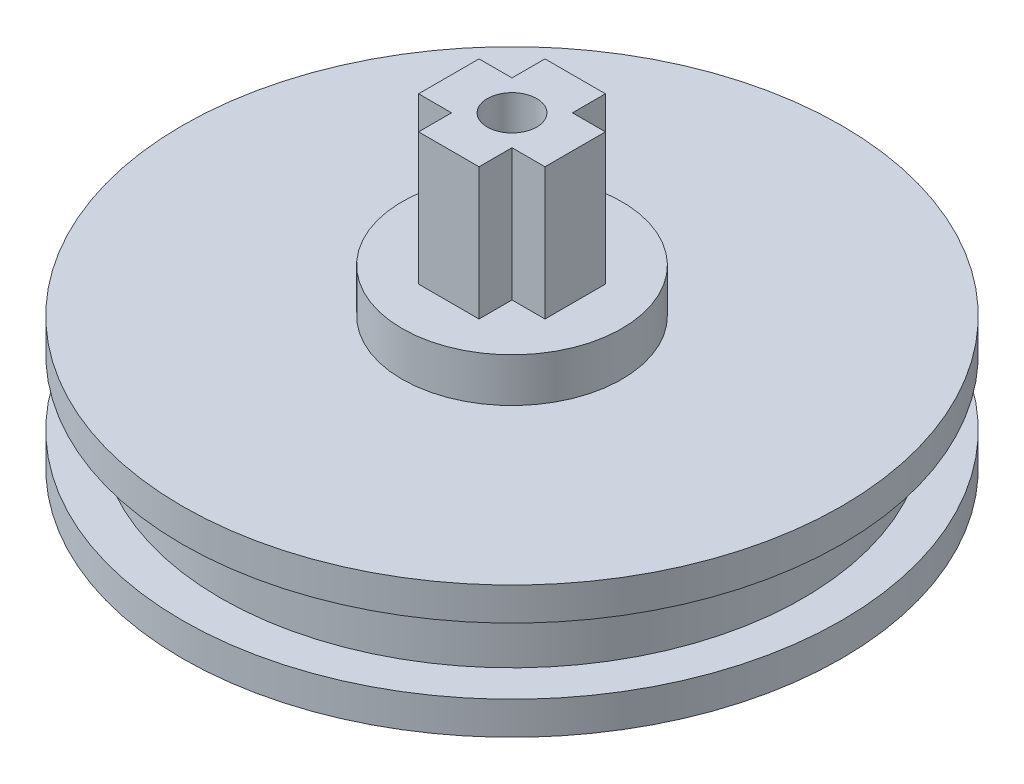
SolidWorks part; units mm, degrees
ref_plane "Front Plane" through (0, 0, 0) normal (0, 0, 1) x (1, 0, 0)
ref_plane "Top Plane" through (0, 0, 0) normal (0, 1, 0) x (1, 0, 0)
ref_plane "Right Plane" through (0, 0, 0) normal (1, 0, 0) x (0, 0, -1)
sketch "Sketch1" plane through (0, 0, 0) normal (0, 1, 0) x (1, 0, 0)
  circle A0 centre (0, 0) radius 30
extrude "c" add sketch "Sketch1" along normal blind 3
sketch "Sketch2" plane through (0, 3, 0) normal (0, 1, 0) x (1, 0, 0)
  circle A0 centre (0, 0) radius 26.5
extrude "Boss-Extrude2" add sketch "Sketch2" along normal blind 6
sketch "Sketch3" plane through (0, 9, 0) normal (0, 1, 0) x (1, 0, 0)
  circle A0 centre (0, 0) radius 30
extrude "Boss-Extrude3" add sketch "Sketch3" along normal blind 3
sketch "Sketch4" plane through (0, 12, 0) normal (0, 1, 0) x (1, 0, 0)
  line L1 (5.75, -2.75) -> (-5.75, -2.75)
  line L2 (5.75, -2.75) -> (5.75, 2.75)
  line L3 (5.75, 2.75) -> (-5.75, 2.75)
  line L4 (-5.75, -2.75) -> (-5.75, 2.75)
  line L5 (5.75, -2.75) -> (-5.75, 2.75) construction
  line L6 (5.75, 2.75) -> (-5.75, -2.75) construction
  line L7 (2.75, -5.75) -> (-2.75, -5.75)
  line L8 (2.75, -5.75) -> (2.75, 5.75)
  line L9 (2.75, 5.75) -> (-2.75, 5.75)
  line L10 (-2.75, -5.75) -> (-2.75, 5.75)
  line L11 (2.75, -5.75) -> (-2.75, 5.75) construction
  line L12 (2.75, 5.75) -> (-2.75, -5.75) construction
  point P0 (0, 0)
  point P6 (0, 0)
  dimension "D1" = 11.5
  dimension "D2" = 5.5
  dimension "D3" = 5.5
  dimension "D4" = 11.5
extrude "Boss-Extrude4" add sketch "Sketch4" along normal blind 16 contours L10 L3 L8 L9 | L1 L10 L3 L4 | L10 L1 L8 L3 | L10 L7 L8 L1 | L8 L1 L2 L3
sketch "Sketch5" plane through (0, 12, 0) normal (0, 1, 0) x (1, 0, 0)
  circle A0 centre (0, 0) radius 10
extrude "Boss-Extrude5" add sketch "Sketch5" along normal blind 4
sketch "Sketch7" plane through (0, 28, 0) normal (0, 1, 0) x (1, 0, 0)
  circle A0 centre (0, 0) radius 2.25
extrude "Cut-Extrude1" cut sketch "Sketch7" against normal blind 46
sketch "Sketch8" plane through (0, 0, 0) normal (0, -1, 0) x (1, 0, 0)
  circle A0 centre (0, 0) radius 6.5
extrude "Cut-Extrude2" cut sketch "Sketch8" against normal blind 3.5
